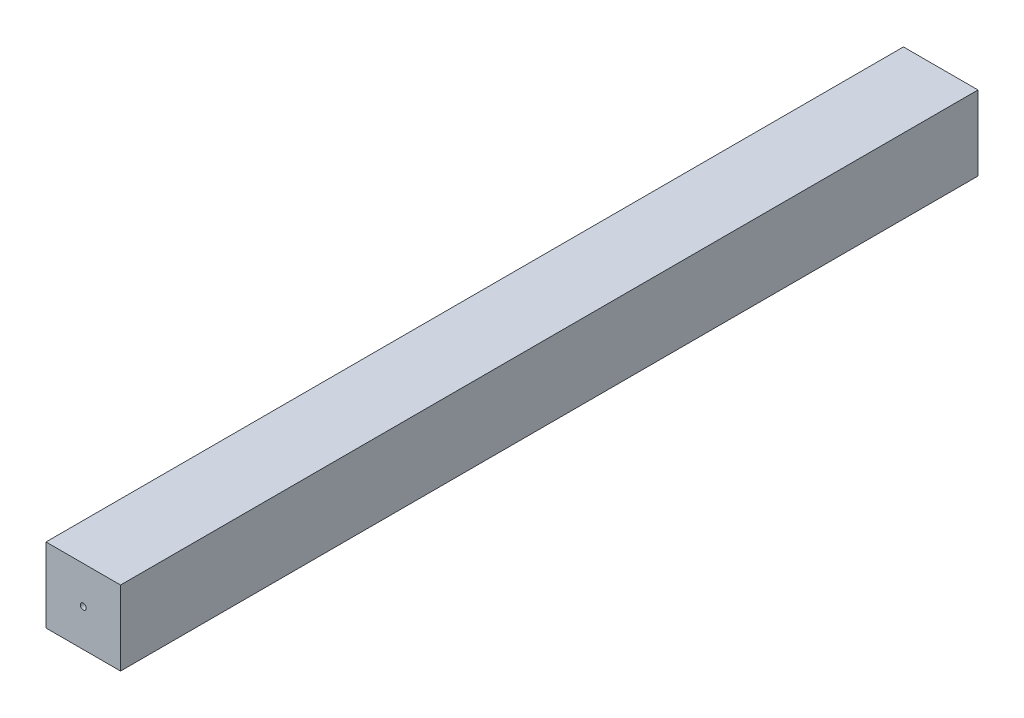
SolidWorks part; units mm, degrees
material "Pin"
ref_plane "Plan de face" through (0, 0, 0) normal (0, 0, 1) x (1, 0, 0)
ref_plane "Plan de dessus" through (0, 0, 0) normal (0, 1, 0) x (1, 0, 0)
ref_plane "Plan de droite" through (0, 0, 0) normal (1, 0, 0) x (0, 0, -1)
sketch "Esquisse1" plane through (0, 0, 0) normal (0, 0, 1) x (1, 0, 0)
  line L1 (22, 22) -> (-22, 22)
  line L2 (22, 22) -> (22, -22)
  line L3 (22, -22) -> (-22, -22)
  line L4 (-22, 22) -> (-22, -22)
  line L5 (22, 22) -> (-22, -22) construction
  line L6 (22, -22) -> (-22, 22) construction
  point P0 (0, 0)
extrude "Boss.-Extru.1" add sketch "Esquisse1" along normal blind 506
sketch "Esquisse2" plane through (0, 0, 0) normal (0, 0, -1) x (-1, 0, 0)
  circle A0 centre (0, 0) radius 1.75
  dimension "D1" = 3.5
extrude "Enlèv. mat.-Extru.1" cut sketch "Esquisse2" against normal blind 60
sketch "Esquisse3" plane through (0, 0, 506) normal (0, 0, 1) x (1, 0, 0)
  circle A0 centre (0, 0) radius 1.75
  dimension "D1" = 3.5
extrude "Enlèv. mat.-Extru.2" cut sketch "Esquisse3" against normal blind 60
